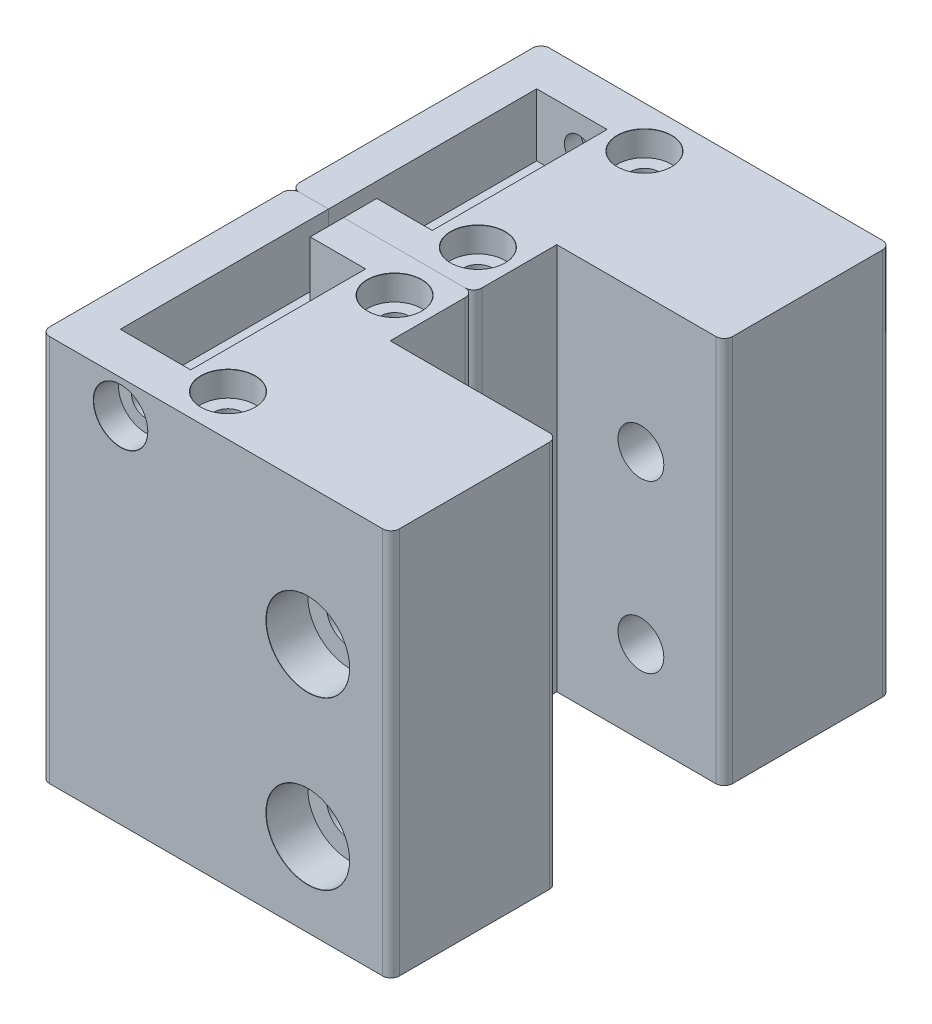
SolidWorks part; units mm, degrees
ref_plane "Front Plane" through (0, 0, 0) normal (0, 0, 1) x (1, 0, 0)
ref_plane "Top Plane" through (0, 0, 0) normal (0, 1, 0) x (1, 0, 0)
ref_plane "Right Plane" through (0, 0, 0) normal (1, 0, 0) x (0, 0, -1)
sketch "Sketch1" plane through (0, 0, 0) normal (0, 1, 0) x (1, 0, 0)
  line L1 (21, 10) -> (-21, 10)
  line L2 (21, 10) -> (21, -10)
  line L3 (21, -10) -> (-21, -10)
  line L4 (-21, 10) -> (-21, -10)
  line L5 (21, 10) -> (-21, -10) construction
  line L6 (21, -10) -> (-21, 10) construction
  point P0 (0, 0)
  dimension "D1" = 20
  dimension "D2" = 42
extrude "Boss-Extrude1" add sketch "Sketch1" along normal blind 40
sketch "Sketch2" plane through (0, 0, 10) normal (0, 0, 1) x (1, 0, 0)
  line L0 (21, 20) -> (-21, 20) construction
  line L3 (21, 40) -> (21, 0) construction
  line L4 (-21, 40) -> (-21, 0) construction
  line L5 (11, 30) -> (11, 10)
  point P9 (11, 20)
  dimension "D1" = 20
  dimension "D2" = 10
hole_wizard "CBORE for M5 SHCS1" positions "Sketch3" profile "Sketch4" counterbore size "M5" standard "ANSI Metric" end condition through all
sketch "Sketch3" plane through (0, 0, 10) normal (0, 0, 1) x (1, 0, 0)
  point P0 (11, 30)
  point P3 (11, 10)
sketch "Sketch4" plane through (11, 30, 10) normal (1, 0, 0) x (0, -1, 0)
  line L0 (0, 0) -> (0, 20)
  line L1 (0, 20) -> (2.75, 20)
  line L3 (2.75, 20) -> (2.75, 5)
  line L4 (5, 5) -> (2.75, 5)
  line L5 (5, 5) -> (5, 0.021)
  line L6 (5, 0.021) -> (5.025, 0)
  line L7 (5.025, 0) -> (0, 0)
  line L8 (-5, 0.021) -> (-5.025, 0) construction
  line L11 (0, -6.35) -> (0, 107.95) construction
  dimension "Thru Hole Dia." = 5.5
  dimension "Thru Hole Depth" = 20
  dimension "C'Bore Dia." = 10
  dimension "C'Bore Depth" = 5
  dimension "Near C'Sink Dia." = 10.05
  dimension "Near C'Sink Angle" = 100
sketch "Sketch5" plane through (0, 40, 0) normal (0, 1, 0) x (1, 0, 0)
  line L4 (-21, 10) -> (-21, -10)
  line L5 (-21, -10) -> (21, -10)
  line L6 (21, -10) -> (21, 10)
  line L7 (21, 10) -> (-21, 10)
  line L8 (-21, 10) -> (-21, -10)
  line L9 (-21, -10) -> (21, -10)
  line L10 (21, -10) -> (21, 10)
  line L11 (21, 10) -> (-21, 10)
  dimension "D1" = 0
extrude "Boss-Extrude2" add sketch "Sketch5" along normal blind 6.5
sketch "Sketch12" plane through (0, 46.5, 0) normal (0, 1, 0) x (1, 0, 0)
  line L0 (21, -10) -> (21, 10) construction
  line L1 (-21, 10) -> (0.9, 10)
  line L2 (-21, 10) -> (-21, 20)
  line L3 (-21, 20) -> (0.9, 20)
  line L4 (0.9, 10) -> (0.9, 20)
  dimension "D1" = 10
  dimension "D2" = 20.1
extrude "Boss-Extrude3" add sketch "Sketch12" against normal up to surface (46.5 mm away) up to face at (0, 0, 0)
sketch "Sketch6" plane through (0, 46.5, 0) normal (0, 1, 0) x (1, 0, 0)
  line L0 (-16.51, 20) -> (-16.51, -5)
  line L2 (-16.51, -5) -> (-8.05, -5)
  line L3 (-8.05, -5) -> (-8.05, 16)
  line L4 (-8.05, 16) -> (-14.71, 16)
  line L5 (-14.71, 16) -> (-14.71, 20)
  line L6 (-21, 20) -> (-21, -10) construction
  line L7 (-16.51, 20) -> (-14.71, 20)
  line L8 (21, -10) -> (-21, -10) construction
  line L9 (0.9, 20) -> (-21, 20) construction
  dimension "D1" = 4.49
  dimension "D2" = 1.8
  dimension "D3" = 5
  dimension "D4" = 8.46
  dimension "D5" = 4
extrude "Cut-Extrude1" cut sketch "Sketch6" against normal blind 7.5
fillet "Fillet1" radius 1 5 edges at (0.9, 23.25, -20) (21, 23.25, 10) (-21, 23.25, -20) (-21, 23.25, 10) (21, 23.25, -10)
sketch "Sketch7" plane through (0, 0, 10) normal (0, 0, 1) x (1, 0, 0)
  circle A0 centre (-11.48, 42.5) radius 1.65 construction
  circle A1 centre (-11.48, 42.5) radius 1.65
hole_wizard "CBORE for M3 SHCS1" positions "Sketch10" profile "Sketch11" counterbore size "M3" standard "ANSI Metric"
sketch "Sketch10" plane through (0, 0, 10) normal (0, 0, 1) x (1, 0, 0)
  point P0 (-11.48, 42.5)
sketch "Sketch11" plane through (-11.48, 42.5, 10) normal (1, 0, 0) x (0, -1, 0)
  line L0 (0, 0) -> (0, 6.0215)
  line L1 (0, 6.0215) -> (1.7, 5)
  line L2 (1.7, 5) -> (1.7, 3)
  line L3 (1.7, 3) -> (3.25, 3)
  line L5 (3.25, 3) -> (3.25, 0.021)
  line L6 (3.25, 0.021) -> (3.275, 0)
  line L7 (3.275, 0) -> (0, 0)
  line L8 (-3.25, 0.021) -> (-3.275, 0) construction
  line L10 (0, 6.0215) -> (-1.7, 5) construction
  line L11 (0, -6.35) -> (0, 107.95) construction
  dimension "Hole Dia." = 3.4
  dimension "Hole Depth" = 5
  dimension "C'Bore Dia." = 6.5
  dimension "C'Bore Depth" = 3
  dimension "Near C'Sink Dia." = 6.55
  dimension "Near C'Sink Angle" = 100
  dimension "Drill Angle" = 118
sketch "Sketch14" plane through (0, 46.5, 0) normal (0, 1, 0) x (1, 0, 0)
  line L0 (-3.575, 20) -> (-3.575, -10) construction
  line L1 (-0.1, 20) -> (-14.71, 20) construction
  line L2 (-20, -10) -> (20, -10) construction
  line L3 (0.9, 10) -> (0.9, 19) construction
  line L4 (-3.575, 15) -> (-3.575, -5) construction
  circle A0 centre (-3.575, 15) radius 2.4
  circle A1 centre (-3.575, -5) radius 2.4
  point P12 (-3.575, 5)
  dimension "D3" = 4.8
  dimension "D1" = 4.475
  dimension "D2" = 20
hole_wizard "CBORE for M3 SHCS2" positions "Sketch17" profile "Sketch16" counterbore size "M3" standard "ANSI Metric" end condition through all
sketch "Sketch17" plane through (0, 46.5, 0) normal (0, 1, 0) x (1, 0, 0)
  point P0 (-3.575, 15)
  point P3 (-3.575, -5)
sketch "Sketch16" plane through (-3.575, 46.5, -15) normal (1, 0, 0) x (0, 0, 1)
  line L0 (0, 0) -> (0, 46.5)
  line L1 (0, 46.5) -> (1.7, 46.5)
  line L3 (1.7, 46.5) -> (1.7, 3)
  line L4 (3.25, 3) -> (1.7, 3)
  line L5 (3.25, 3) -> (3.25, 0.021)
  line L6 (3.25, 0.021) -> (3.275, 0)
  line L7 (3.275, 0) -> (0, 0)
  line L8 (-3.25, 0.021) -> (-3.275, 0) construction
  line L11 (0, -6.35) -> (0, 107.95) construction
  dimension "Thru Hole Dia." = 3.4
  dimension "Thru Hole Depth" = 46.5
  dimension "C'Bore Dia." = 6.5
  dimension "C'Bore Depth" = 3
  dimension "Near C'Sink Dia." = 6.55
  dimension "Near C'Sink Angle" = 100
sketch "Sketch18" plane through (0, 0, 0) normal (0, -1, 0) x (1, 0, 0)
  line L1 (-0.475, 5) -> (-2.025, 7.6847)
  line L2 (-2.025, 7.6847) -> (-5.125, 7.6847)
  line L3 (-5.125, 7.6847) -> (-6.675, 5)
  line L4 (-6.675, 5) -> (-5.125, 2.3153)
  line L5 (-5.125, 2.3153) -> (-2.025, 2.3153)
  line L6 (-2.025, 2.3153) -> (-0.475, 5)
  line L7 (-0.475, -15) -> (-2.025, -12.3153)
  line L8 (-2.025, -12.3153) -> (-5.125, -12.3153)
  line L9 (-5.125, -12.3153) -> (-6.675, -15)
  line L10 (-6.675, -15) -> (-5.125, -17.6847)
  line L11 (-5.125, -17.6847) -> (-2.025, -17.6847)
  line L12 (-2.025, -17.6847) -> (-0.475, -15)
  line L14 (-20, 10) -> (20, 10) construction
  circle A0 centre (-3.575, 5) radius 2.6847 construction
  circle A1 centre (-3.575, -15) radius 2.6847 construction
  dimension "D1" = 3.1
extrude "Cut-Extrude2" cut sketch "Sketch18" against normal blind 8
mirror "Mirror1" about plane through (-21, -24.0751, -20) normal (0, 0, -1) of bodies 111
